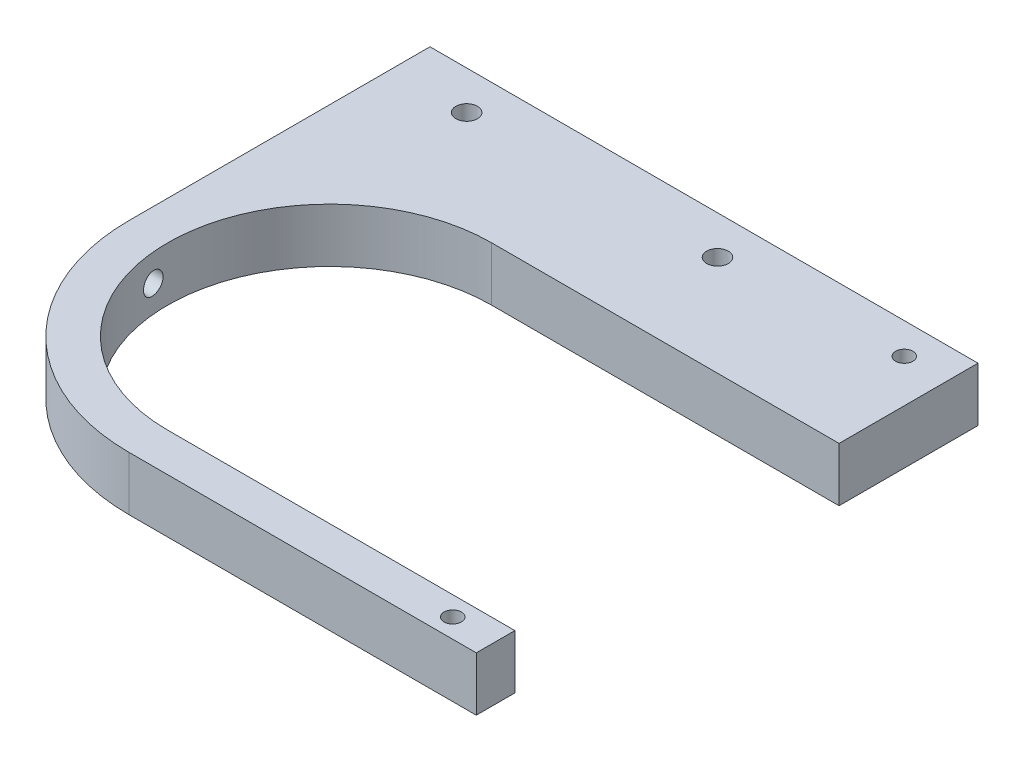
SolidWorks part; units mm, degrees
ref_plane "정면" through (0, 0, 0) normal (0, 0, 1) x (1, 0, 0)
ref_plane "윗면" through (0, 0, 0) normal (0, 1, 0) x (1, 0, 0)
ref_plane "우측면" through (0, 0, 0) normal (1, 0, 0) x (0, 0, -1)
sketch "스케치1" plane through (0, 0, 0) normal (0, 1, 0) x (1, 0, 0)
  line L0 (0, 21) -> (45, 21)
  line L2 (0, -21) -> (45, -21)
  line L3 (45, 21) -> (45, 39)
  line L4 (45, 39) -> (-26, 39)
  line L5 (-26, 39) -> (-26, 0)
  line L6 (0, -26) -> (45, -26)
  line L7 (45, -26) -> (45, -21)
  arc A0 (0, 21) -> (0, -21) centre (0, 0) ccw
  arc A1 (-26, 0) -> (0, -26) centre (0, 0) ccw
  dimension "D1" = 45
  dimension "D2" = 42
  dimension "D3" = 71
  dimension "D4" = 18
  dimension "D5" = 5
extrude "보스-돌출1" add sketch "스케치1" along normal blind 7
sketch "스케치2" plane through (0, 7, 0) normal (0, 1, 0) x (1, 0, 0)
  line L0 (0, -26) -> (45, -26) construction
  line L1 (45, 39) -> (35, 39) construction
  line L2 (45, 39) -> (45, -26) construction
  line L3 (45, -26) -> (35, -26) construction
  line L4 (35, 39) -> (35, -26) construction
  circle A0 centre (39.4458, 35) radius 1.125
  circle A1 centre (39.4458, -23.5) radius 1.125
  point P11 (40, 39)
  dimension "D2" = 2.25
  dimension "D3" = 2.25
  dimension "D5" = 2.5
  dimension "D1" = 10
  dimension "D4" = 4
extrude "컷-돌출2" cut sketch "스케치2" against normal through all and the other way through all
ref_plane "평면1" through (-26, 0, 0) normal (-1, 0, 0) x (0, 0, 1)
sketch "스케치4" plane through (-26, 0, 0) normal (-1, 0, 0) x (0, 0, 1)
  line L0 (-39, 0) -> (1.9862, 0) construction
  line L1 (-39, 7) -> (-39, 0) construction
  line L2 (-39, 0) -> (0, 0) construction
  line L3 (1.9862, 0) -> (1.9862, 3.5) construction
  circle A0 centre (1.9862, 3.5) radius 1.4
  dimension "D2" = 2.8
  dimension "D1" = 3.5
extrude "컷-돌출3" cut sketch "스케치4" against normal through all
sketch "스케치5" plane through (0, 7, 0) normal (0, 1, 0) x (1, 0, 0)
  line L0 (20, 0) -> (20, 58) construction
  line L1 (-20, 0) -> (-20, 56.7641) construction
  line L3 (-20, 39) -> (20, 39) construction
  line L4 (-20, 39) -> (-20, 29) construction
  line L5 (-20, 29) -> (20, 29) construction
  line L6 (20, 39) -> (20, 29) construction
  line L7 (45, 39) -> (-26, 39) construction
  line L8 (0, 0) -> (0, 56.7641) construction
  circle A0 centre (0, 0) radius 22.5 construction
  circle A1 centre (16.25, 34) radius 1.4
  circle A2 centre (-16.25, 34) radius 1.4
  dimension "D1" = 10
  dimension "D5" = 2.8
  dimension "D6" = 2.8
  dimension "D9" = 5
  dimension "D2" = 0
  dimension "D3" = 20
  dimension "D4" = 20
  dimension "D7" = 3.75
  dimension "D8" = 3.75
  dimension "D10" = 5
extrude "컷-돌출4" cut sketch "스케치5" against normal through all
